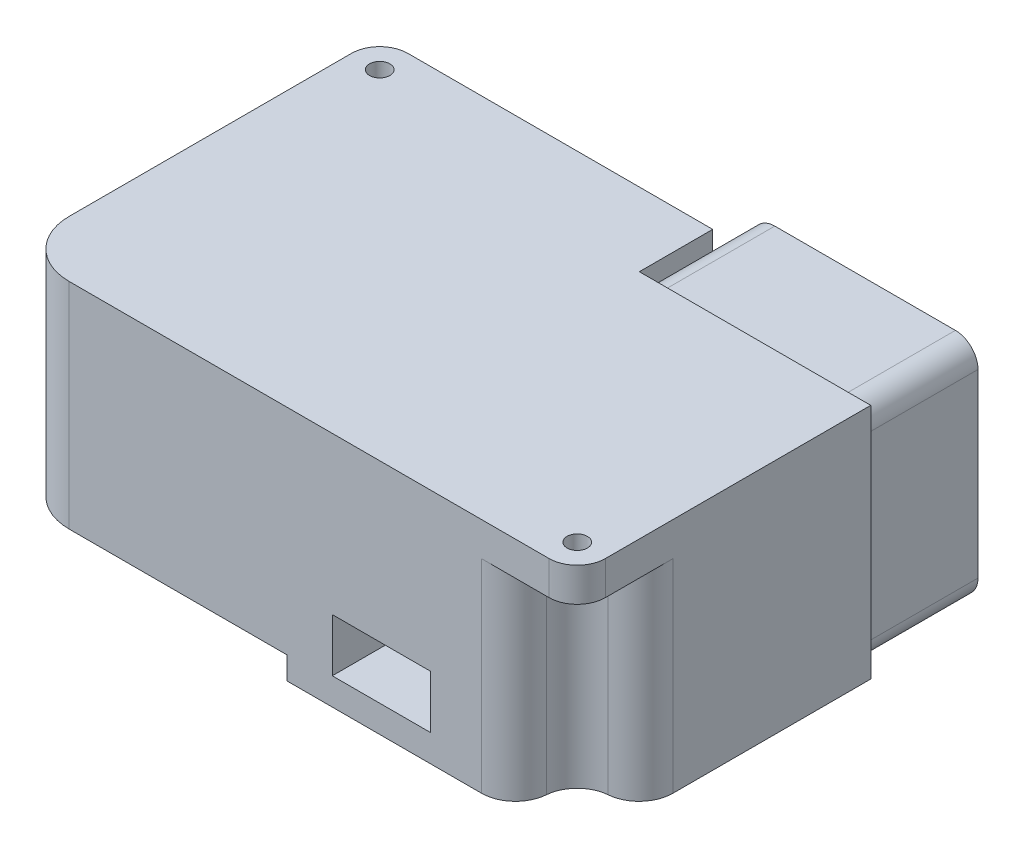
SolidWorks part; units mm, degrees
ref_plane "前视基准面" through (0, 0, 0) normal (0, 0, 1) x (1, 0, 0)
ref_plane "上视基准面" through (0, 0, 0) normal (0, 1, 0) x (1, 0, 0)
ref_plane "右视基准面" through (0, 0, 0) normal (1, 0, 0) x (0, 0, -1)
sketch "草图1" plane through (0, 0, 0) normal (0, 1, 0) x (1, 0, 0)
  line L0 (4.5, 16.25) -> (4.5, 9.75)
  line L1 (22.5, -16.25) -> (-20, -16.25)
  line L2 (25, -13.75) -> (25, 9.75)
  line L3 (4.5, 16.25) -> (-22.5, 16.25)
  line L4 (-25, -11.25) -> (-25, 13.75)
  line L5 (25, -16.25) -> (-25, 16.25) construction
  line L6 (25, 16.25) -> (-25, -16.25) construction
  line L7 (4.5, 9.75) -> (25, 9.75)
  circle A0 centre (-22.5, 13.75) radius 0.9
  circle A1 centre (22.5, -13.75) radius 0.9
  arc A2 (25, -13.75) -> (22.5, -16.25) centre (22.5, -13.75) cw
  arc A3 (-22.5, 16.25) -> (-25, 13.75) centre (-22.5, 13.75) ccw
  arc A4 (-25, -11.25) -> (-20, -16.25) centre (-20, -11.25) ccw
  point P0 (0, 0)
  dimension "D3" = 1.8
  dimension "D8" = 2.5
  dimension "D9" = 5
  dimension "D1" = 32.5
  dimension "D2" = 50
  dimension "D4" = 2.5
  dimension "D5" = 2.5
  dimension "D6" = 2.5
  dimension "D7" = 2.5
  dimension "D10" = 20.5
  dimension "D11" = 6.5
extrude "凸台-拉伸1" add sketch "草图1" along normal blind 3
sketch "草图2" plane through (0, 3, 0) normal (0, 1, 0) x (1, 0, 0)
  line L46 (4.5, 16.25) -> (-22.5, 16.25)
  line L47 (4.5, 9.75) -> (4.5, 16.25)
  line L48 (25, 9.75) -> (4.5, 9.75)
  line L49 (25, -13.75) -> (25, 9.75)
  line L50 (-20, -16.25) -> (22.5, -16.25)
  line L51 (-25, 13.75) -> (-25, -11.25)
  line L52 (4.5, 16.25) -> (-16.5209, 16.25)
  line L53 (4.5, 9.75) -> (4.5, 16.25)
  line L54 (25, 9.75) -> (4.5, 9.75)
  line L55 (25, -7.7709) -> (25, 9.75)
  line L56 (-20, -16.25) -> (16.5209, -16.25)
  line L57 (-25, 7.7709) -> (-25, -11.25)
  arc A0 (-22.25, 10.7604) -> (-19.5104, 13.5) centre (-22.5, 13.75) ccw
  arc A1 (-22.25, 10.7604) -> (-25, 7.7709) centre (-22, 7.7709) ccw
  arc A2 (-16.5209, 16.25) -> (-19.5104, 13.5) centre (-16.5209, 13.25) ccw
  arc A3 (22.25, -10.7604) -> (19.5104, -13.5) centre (22.5, -13.75) ccw
  arc A4 (19.5104, -13.5) -> (16.5209, -16.25) centre (16.5209, -13.25) cw
  arc A5 (25, -7.7709) -> (22.25, -10.7604) centre (22, -7.7709) cw
  arc A15 (22.5, -16.25) -> (25, -13.75) centre (22.5, -13.75) ccw
  arc A16 (-22.5, 16.25) -> (-25, 13.75) centre (-22.5, 13.75) ccw
  arc A17 (-25, -11.25) -> (-20, -16.25) centre (-20, -11.25) ccw
  arc A20 (-25, -11.25) -> (-20, -16.25) centre (-20, -11.25) ccw
  dimension "D2" = 3
  dimension "D3" = 3
  dimension "D4" = 3
  dimension "D5" = 3
  dimension "D6" = 3
  dimension "D7" = 3
  dimension "D1" = 0
extrude "凸台-拉伸2" add sketch "草图2" against normal blind 19
sketch "草图4" plane through (0, -16, 0) normal (0, -1, 0) x (1, 0, 0)
  line L18 (-0.7, -16.25) -> (-0.7, 16.25)
  line L23 (4.5, -16.25) -> (-16.5209, -16.25)
  line L24 (4.5, -9.75) -> (4.5, -16.25)
  line L25 (25, -9.75) -> (4.5, -9.75)
  line L26 (-20, 16.25) -> (16.5209, 16.25)
  line L27 (25, 7.7709) -> (25, -9.75)
  line L28 (4.5, -16.25) -> (-0.7, -16.25)
  line L29 (4.5, -9.75) -> (4.5, -16.25)
  line L30 (25, -9.75) -> (4.5, -9.75)
  line L31 (-0.7, 16.25) -> (16.5209, 16.25)
  line L32 (25, 7.7709) -> (25, -9.75)
  arc A21 (19.5104, 13.5) -> (16.5209, 16.25) centre (16.5209, 13.25) ccw
  arc A22 (19.5104, 13.5) -> (22.25, 10.7604) centre (22.5, 13.75) ccw
  arc A23 (25, 7.7709) -> (22.25, 10.7604) centre (22, 7.7709) ccw
  arc A24 (19.5104, 13.5) -> (16.5209, 16.25) centre (16.5209, 13.25) ccw
  arc A25 (19.5104, 13.5) -> (22.25, 10.7604) centre (22.5, 13.75) ccw
  arc A26 (25, 7.7709) -> (22.25, 10.7604) centre (22, 7.7709) ccw
  dimension "D2" = 5.2
  dimension "D1" = 0
extrude "凸台-拉伸3" add sketch "草图4" along normal blind 2
sketch "草图5" plane through (0, 0, 16.25) normal (0, 0, 1) x (1, 0, 0)
  line L0 (16.5209, -18) -> (-0.7, -18) construction
  line L1 (12, -15.6) -> (3.3, -15.6)
  line L2 (12, -15.6) -> (12, -10.9)
  line L3 (12, -10.9) -> (3.3, -10.9)
  line L4 (3.3, -15.6) -> (3.3, -10.9)
  line L5 (25, -18) -> (25, 0) construction
  dimension "D1" = 8.7
  dimension "D2" = 4.7
  dimension "D3" = 2.4
  dimension "D4" = 13
extrude "切除-拉伸1" cut sketch "草图5" against normal blind 6.3
sketch "草图6" plane through (0, 0, -9.75) normal (0, 0, -1) x (-1, 0, 0)
  line L0 (-4.5, 3) -> (-4.5, -18) construction
  line L1 (-6.5, 2.5) -> (-22.5, 2.5)
  line L2 (-4.5, 0.5) -> (-4.5, -15.5)
  line L3 (-6.5, -17.5) -> (-22.5, -17.5)
  line L4 (-24.5, 0.5) -> (-24.5, -15.5)
  line L5 (-25, 3) -> (-4.5, 3) construction
  line L6 (-6.5, 0.5) -> (-22.5, -15.5) construction
  line L7 (-6.5, -15.5) -> (-22.5, 0.5) construction
  line L8 (-14.5, -13.75) -> (-12.0341, -16.4671)
  line L9 (-14.5, -16.8) -> (-19.1282, -11.7003)
  line L10 (-19.9127, -4.375) -> (-23.4987, -5.152)
  line L11 (-22.554, -2.85) -> (-15.8234, -1.3917)
  line L12 (-9.0873, -4.375) -> (-7.9672, -0.8809)
  line L13 (-6.446, -2.85) -> (-8.5484, -9.408)
  arc A0 (-22.5, 2.5) -> (-24.5, 0.5) centre (-22.5, 0.5) ccw
  arc A1 (-22.5, -17.5) -> (-24.5, -15.5) centre (-22.5, -15.5) cw
  arc A2 (-4.5, -15.5) -> (-6.5, -17.5) centre (-6.5, -15.5) cw
  arc A3 (-4.5, 0.5) -> (-6.5, 2.5) centre (-6.5, 0.5) ccw
  arc A4 (-12.0341, -16.4671) -> (-6.446, -2.85) centre (-14.5, -7.5) ccw
  arc A5 (-14.5, -13.75) -> (-8.5484, -9.408) centre (-14.5, -7.5) ccw
  arc A6 (-9.0873, -4.375) -> (-15.8234, -1.3917) centre (-14.5, -7.5) ccw
  arc A7 (-7.9672, -0.8809) -> (-22.554, -2.85) centre (-14.5, -7.5) ccw
  arc A8 (-23.4987, -5.152) -> (-14.5, -16.8) centre (-14.5, -7.5) ccw
  arc A9 (-19.9127, -4.375) -> (-19.1282, -11.7003) centre (-14.5, -7.5) ccw
  point P16 (-4.5, 2.5)
  point P35 (-14.5, -7.5)
  dimension "D3" = 2
  dimension "D4" = 18.6
  dimension "D5" = 12.5
  dimension "D1" = 20
  dimension "D2" = 0.5
  dimension "D6" = 3
extrude "凸台-拉伸4" add sketch "草图6" along normal blind 10
